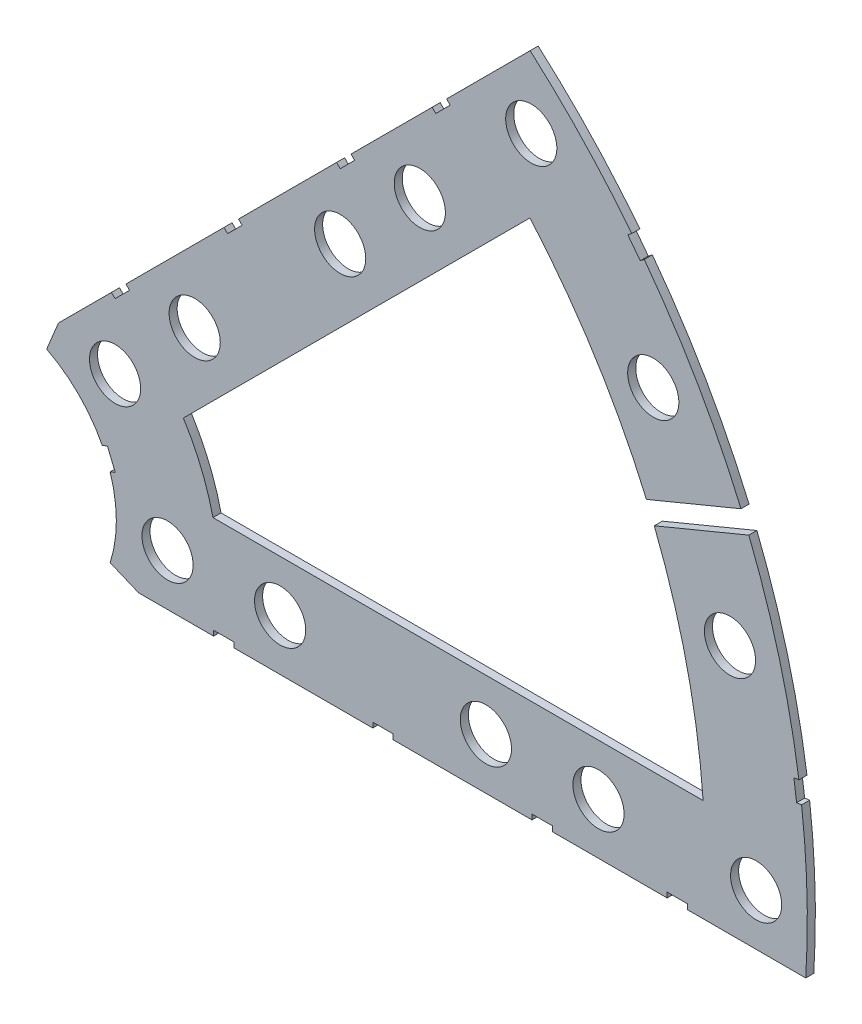
SolidWorks part; units mm, degrees
material "Copper"
ref_plane "Front Plane" through (0, 0, 0) normal (0, 0, 1) x (1, 0, 0)
ref_plane "Top Plane" through (0, 0, 0) normal (0, 1, 0) x (1, 0, 0)
ref_plane "Right Plane" through (0, 0, 0) normal (1, 0, 0) x (0, 0, -1)
sketch "Sketch1" plane through (0, 0, 0) normal (0, 0, 1) x (1, 0, 0)
  line L0 (0, 0) -> (320.3893, 0) construction
  line L1 (0, 0) -> (155.5285, 155.5285) construction
  line L2 (67.2115, 76.1917) -> (8.6967, 17.6769)
  line L3 (8.6967, 17.6769) -> (7.229, 14.1336)
  line L4 (101.4014, -6.35) -> (18.6489, -6.35)
  line L5 (15.1056, -4.8823) -> (18.6489, -6.35)
  line L6 (88.6729, 6.35) -> (27.8605, 6.35)
  line L9 (67.1914, 58.2111) -> (24.1905, 15.2102)
  line L10 (0, 0) -> (40.4486, 97.6516) construction
  line L11 (0, 0) -> (123.4567, -51.1374) construction
  line L18 (8.6967, 17.6769) -> (13.294, 8.6183) construction
  line L19 (18.6489, -6.35) -> (15.4943, 3.3063) construction
  line L20 (27.8605, 6.35) -> (27.7442, 6.7059) construction
  line L21 (24.1905, 15.2102) -> (24.3599, 14.8764) construction
  arc A0 (7.229, 14.1336) -> (15.1056, -4.8823) centre (0, 0) cw
  arc A1 (67.2115, 76.1917) -> (101.4014, -6.35) centre (0, 0) cw
  arc A2 (24.1905, 15.2102) -> (27.8605, 6.35) centre (0, 0) cw
  arc A3 (67.1914, 58.2111) -> (88.6729, 6.35) centre (0, 0) cw
  arc A8 (13.294, 8.6183) -> (15.4943, 3.3063) centre (0, 0) cw construction
  arc A9 (24.3599, 14.8764) -> (27.7442, 6.7059) centre (0, 0) cw construction
  dimension "D1" = 45
  dimension "D3" = 6.35
  dimension "D4" = 15.875
  dimension "D7" = 22.5
  dimension "D8" = 101.6
  dimension "D11" = 12.7
  dimension "D12" = 12.7
  dimension "D2" = 6.35
  dimension "D5" = 67.5
  dimension "D9" = 1.27
  dimension "D10" = 1.27
  dimension "D6" = 12.7
extrude "Boss-Extrude1" add sketch "Sketch1" along normal blind 1
sketch "Sketch2" plane through (0, 0, 1) normal (0, 0, 1) x (1, 0, 0)
  line L0 (0, 0) -> (101.6, 0) construction
  line L1 (0, 0) -> (71.842, 71.842) construction
  line L3 (0, 0) -> (22.225, 0) construction
  line L4 (0, 0) -> (15.7154, 15.7154) construction
  line L5 (0, 0) -> (95.25, 0) construction
  line L6 (0, 0) -> (92.0044, 24.6525) construction
  arc A0 (101.4014, -6.35) -> (67.2115, 76.1917) centre (0, 0) ccw construction
  circle A1 centre (22.225, 0) radius 3.175
  arc A2 (15.1056, -4.8823) -> (7.229, 14.1336) centre (0, 0) ccw construction
  circle A3 centre (36.195, 0) radius 3.175
  circle A4 centre (61.722, 0) radius 3.175
  circle A5 centre (75.692, 0) radius 3.175
  circle A6 centre (95.25, 0) radius 3.175
  circle A7 centre (15.7154, 15.7154) radius 3.175
  circle A8 centre (25.5937, 25.5937) radius 3.175
  circle A9 centre (43.644, 43.644) radius 3.175
  circle A10 centre (53.5223, 53.5223) radius 3.175
  circle A11 centre (92.0044, 24.6525) radius 3.175
  circle A12 centre (82.4889, 47.625) radius 3.175
  circle A13 centre (67.3519, 67.3519) radius 3.175
  dimension "D3" = 6.35
  dimension "D1" = 45
  dimension "D2" = 6.35
  dimension "D4" = 6.35
  dimension "D5" = 13.97
  dimension "D7" = 13.97
  dimension "D8" = 19.558
  dimension "D9" = 45
  dimension "D10" = 15
  dimension "D11" = 25.527
  dimension "D6" = 2
extrude "Cut-Extrude1" cut sketch "Sketch2" against normal through all
sketch "Sketch3" plane through (0, 0, 1) normal (0, 0, 1) x (1, 0, 0)
  line L0 (15.2664, 24.2467) -> (17.0625, 26.0427)
  line L1 (15.2664, 24.2467) -> (15.7154, 23.7977)
  line L2 (17.0625, 26.0427) -> (17.5115, 25.5937)
  line L3 (15.7154, 23.7977) -> (17.5115, 25.5937)
  line L4 (67.2115, 76.1917) -> (8.6967, 17.6769) construction
  line L5 (44.9911, 53.9713) -> (43.195, 52.1753)
  line L6 (44.9911, 53.9713) -> (45.4401, 53.5223)
  line L7 (43.195, 52.1753) -> (43.644, 51.7263)
  line L8 (45.4401, 53.5223) -> (43.644, 51.7263)
  line L9 (27.94, -6.35) -> (30.48, -6.35)
  line L10 (27.94, -6.35) -> (27.94, -5.715)
  line L11 (30.48, -6.35) -> (30.48, -5.715)
  line L12 (27.94, -5.715) -> (30.48, -5.715)
  line L13 (18.6489, -6.35) -> (101.4014, -6.35) construction
  line L14 (67.437, -6.35) -> (69.977, -6.35)
  line L15 (67.437, -6.35) -> (67.437, -5.715)
  line L16 (69.977, -6.35) -> (69.977, -5.715)
  line L17 (67.437, -5.715) -> (69.977, -5.715)
  line L18 (29.2307, 38.211) -> (31.0268, 40.007)
  line L19 (29.2307, 38.211) -> (29.6797, 37.762)
  line L20 (31.0268, 40.007) -> (31.4758, 39.558)
  line L21 (29.6797, 37.762) -> (31.4758, 39.558)
  line L22 (56.845, 65.8253) -> (55.049, 64.0292)
  line L23 (56.845, 65.8253) -> (57.294, 65.3763)
  line L24 (55.049, 64.0292) -> (55.498, 63.5802)
  line L25 (57.294, 65.3763) -> (55.498, 63.5802)
  line L26 (47.6885, -6.35) -> (50.2285, -6.35)
  line L27 (47.6885, -6.35) -> (47.6885, -5.715)
  line L28 (50.2285, -6.35) -> (50.2285, -5.715)
  line L29 (47.6885, -5.715) -> (50.2285, -5.715)
  line L30 (84.201, -6.35) -> (86.741, -6.35)
  line L31 (84.201, -6.35) -> (84.201, -5.715)
  line L32 (86.741, -6.35) -> (86.741, -5.715)
  line L33 (84.201, -5.715) -> (86.741, -5.715)
  line L34 (0, 0) -> (100.7308, 13.2615) construction
  line L35 (0, 0) -> (93.8662, 38.8806) construction
  line L36 (0, 0) -> (80.6047, 61.8502) construction
  line L37 (0, 0) -> (101.6, 0) construction
  line L38 (99.9355, 14.4377) -> (100.267, 11.9194)
  line L39 (99.9355, 14.4377) -> (101.1946, 14.6035)
  line L40 (100.267, 11.9194) -> (101.5261, 12.0852)
  line L41 (101.1946, 14.6035) -> (101.5261, 12.0852)
  line L42 (99.9355, 14.4377) -> (101.5261, 12.0852) construction
  line L43 (100.267, 11.9194) -> (101.1946, 14.6035) construction
  line L44 (94.5535, 40.54) -> (95.5255, 38.1933)
  line L45 (94.5535, 40.54) -> (80.4736, 34.7079)
  line L46 (95.5255, 38.1933) -> (81.4456, 32.3612)
  line L47 (80.4736, 34.7079) -> (81.4456, 32.3612)
  line L50 (79.3278, 62.4712) -> (80.874, 60.456)
  line L51 (79.3278, 62.4712) -> (80.3354, 63.2443)
  line L52 (80.874, 60.456) -> (81.8816, 61.2292)
  line L53 (80.3354, 63.2443) -> (81.8816, 61.2292)
  line L54 (79.3278, 62.4712) -> (81.8816, 61.2292) construction
  line L55 (80.874, 60.456) -> (80.3354, 63.2443) construction
  line L56 (13.5939, 7.0054) -> (14.5659, 4.6588)
  line L57 (13.5939, 7.0054) -> (14.7672, 7.4914)
  line L58 (14.5659, 4.6588) -> (15.7393, 5.1448)
  line L59 (14.7672, 7.4914) -> (15.7393, 5.1448)
  line L60 (13.5939, 7.0054) -> (15.7393, 5.1448) construction
  line L61 (14.5659, 4.6588) -> (14.7672, 7.4914) construction
  circle A0 centre (15.7154, 15.7154) radius 3.175 construction
  circle A1 centre (43.644, 43.644) radius 3.175 construction
  circle A2 centre (22.225, 0) radius 3.175 construction
  circle A3 centre (61.722, 0) radius 3.175 construction
  arc A4 (101.4014, -6.35) -> (67.2115, 76.1917) centre (0, 0) ccw construction
  arc A9 (15.1056, -4.8823) -> (7.229, 14.1336) centre (0, 0) ccw construction
  circle A10 centre (36.195, 0) radius 3.175 construction
  circle A11 centre (75.692, 0) radius 3.175 construction
  circle A12 centre (25.5937, 25.5937) radius 3.175 construction
  circle A13 centre (53.5223, 53.5223) radius 3.175 construction
  point P75 (14.6666, 6.0751)
  dimension "D2" = 5.715
  dimension "D3" = 2.54
  dimension "D6" = 5.715
  dimension "D8" = 0.635
  dimension "D9" = 5.715
  dimension "D12" = 5.715
  dimension "D4" = 7.5
  dimension "D5" = 22.5
  dimension "D7" = 37.5
  dimension "D10" = 90
  dimension "D11" = 1.27
  dimension "D14" = 0.635
  dimension "D19" = 90
  dimension "D22" = 0.635
  dimension "D20" = 1.27
  dimension "D17" = 0.635
  dimension "D15" = 2.54
  dimension "D18" = 15.24
  dimension "D21" = 1.27
  dimension "D25" = 1.27
  dimension "D13" = 11.4935
  dimension "D16" = 8.509
  dimension "D23" = 11.4935
  dimension "D24" = 8.509
extrude "Cut-Extrude2" cut sketch "Sketch3" against normal through all
equation "\"cSep\"= 1.005"
equation "\"D11@Sketch2\"=\"cSep\""
equation "\"cSep2\"= \"D8@Sketch2\""
equation "\"D13@Sketch3\"=\"cSep\"/2-.05"
equation "\"D16@Sketch3\"=\"cSep2\"/2-.05"
equation "\"D23@Sketch3\"=\"cSep\"/2-.05"
equation "\"D24@Sketch3\"=\"cSep2\"/2-.05"
